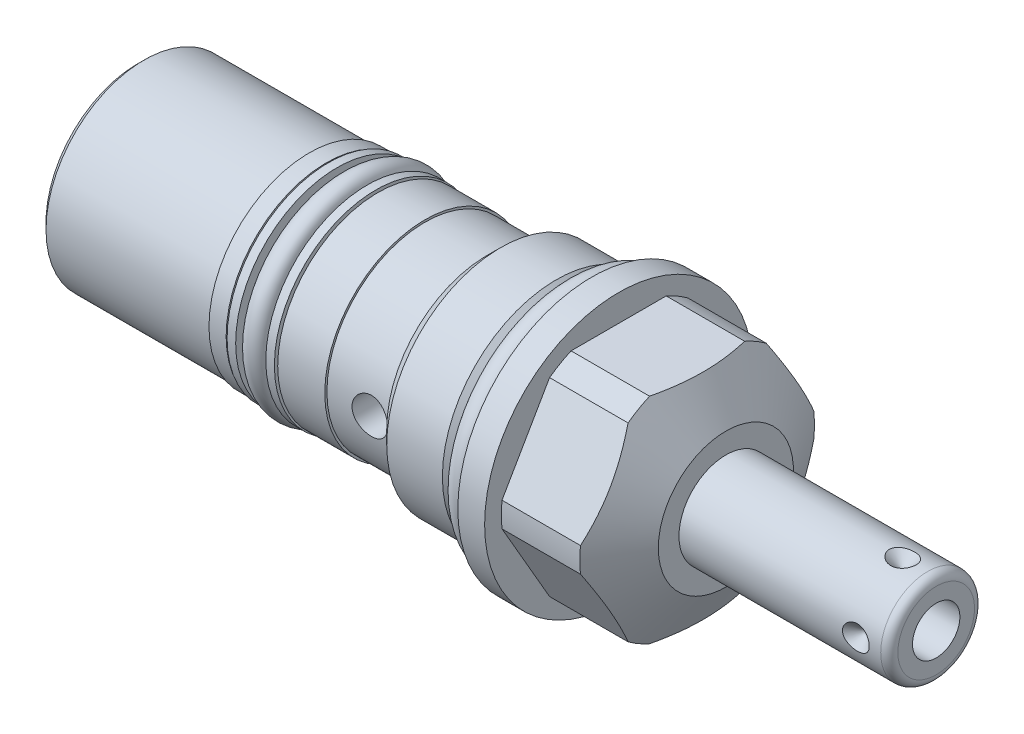
SolidWorks part; units mm, degrees
material "Alloy Steel"
ref_plane "Front Plane" through (0, 0, 0) normal (0, 0, 1) x (1, 0, 0)
ref_plane "Top Plane" through (0, 0, 0) normal (0, 1, 0) x (1, 0, 0)
ref_plane "Right Plane" through (0, 0, 0) normal (1, 0, 0) x (0, 0, -1)
ref_plane "Plane1" through (0, 0, 0) normal (1, 0, 0) x (0, 0, -1)
sketch "Sketch1" plane through (0, 0, 0) normal (1, 0, 0) x (0, 0, -1)
  circle A0 centre (0, 0) radius 15.875
  dimension "D1" = 31.75
extrude "Extrude1" add sketch "Sketch1" along normal blind 15.875 and the other way blind 53.7972
ref_plane "Plane2" through (0, 0, 0) normal (1, 0, 0) x (0, 0, -1)
sketch "Sketch2" plane through (0, 0, 0) normal (1, 0, 0) x (0, 0, -1)
  circle A0 centre (0, 0) radius 13.4937
  circle A1 centre (0, 0) radius 15.875 construction
  circle A2 centre (0, 0) radius 15.875
  dimension "D1" = 26.9875
extrude "Cut-Extrude1" cut sketch "Sketch2" against normal up to next
ref_plane "Plane3" through (0, 0, 0) normal (0, 0, 1) x (1, 0, 0)
sketch "Sketch3" plane through (0, 0, 0) normal (0, 0, 1) x (1, 0, 0)
  line L0 (11.3289, 15.875) -> (15.875, 8.001)
  line L1 (-8.1458, 0) -> (17.0188, 0) construction
  line L2 (15.875, 8.001) -> (15.875, 15.875)
  line L3 (15.875, 15.875) -> (11.3289, 15.875)
  line L4 (15.875, 15.875) -> (0, 15.875) construction
  dimension "D1" = 16.002
  dimension "D2" = 30
revolve "Cut-Revolve1" cut sketch "Sketch3" angle 360 about L1
ref_plane "Plane5" through (3.175, 0, 0) normal (-1, 0, 0) x (0, 0, 1)
sketch "Sketch5" plane through (3.175, 0, 0) normal (-1, 0, 0) x (0, 0, 1)
  line L0 (-7.3323, 12.7) -> (7.3323, 12.7)
  line L1 (7.3323, 12.7) -> (14.6647, 0)
  line L2 (14.6647, 0) -> (7.3323, -12.7)
  line L3 (7.3323, -12.7) -> (-7.3323, -12.7)
  line L4 (-7.3323, -12.7) -> (-14.6647, 0)
  line L5 (-14.6647, 0) -> (-7.3323, 12.7)
  line L6 (0, 0) -> (18.7904, 0) construction
  line L7 (0, 0) -> (7.3323, 12.7) construction
  line L8 (0, 0) -> (-7.3323, 12.7) construction
  circle A0 centre (0, 0) radius 15.875 construction
  circle A1 centre (0, 0) radius 15.875
  dimension "D1" = 25.4
  dimension "D2" = 120
  dimension "D3" = 60
extrude "Cut-Extrude3" cut sketch "Sketch5" against normal up to next
ref_plane "Plane7" through (3.175, 0, 0) normal (-1, 0, 0) x (0, 0, 1)
sketch "Sketch7" plane through (3.175, 0, 0) normal (-1, 0, 0) x (0, 0, 1)
  circle A0 centre (0, 0) radius 13.8938
  circle A1 centre (0, 0) radius 15.875 construction
  circle A2 centre (0, 0) radius 15.875
  dimension "D1" = 27.7876
extrude "Cut-Extrude5" cut sketch "Sketch7" against normal up to next
ref_plane "Plane9" through (0, 0, 0) normal (0, 0, 1) x (1, 0, 0)
sketch "Sketch9" plane through (0, 0, 0) normal (0, 0, 1) x (1, 0, 0)
  line L0 (0, 13.4937) -> (0, 12.0015)
  line L1 (0, 12.0015) -> (-2.7178, 12.0015)
  line L2 (-2.7178, 12.0015) -> (-4.21, 13.4937)
  line L3 (-4.4206, 0) -> (0.2105, 0) construction
  line L4 (0, 13.4937) -> (-4.21, 13.4937)
  line L5 (0, 13.4937) -> (-53.7972, 13.4937) construction
  line L6 (0, 15.875) -> (0, -15.875) construction
  dimension "D1" = 2.7178
  dimension "D2" = 45
  dimension "D3" = 24.003
revolve "Cut-Revolve3" cut sketch "Sketch9" angle 360 about L3
ref_plane "Plane10" through (0, 0, 0) normal (0, 0, 1) x (1, 0, 0)
sketch "Sketch10" plane through (0, 0, 0) normal (0, 0, 1) x (1, 0, 0)
  line L0 (-10.8013, 13.4937) -> (-12.4206, 11.8745)
  line L1 (-12.4206, 11.8745) -> (-53.7972, 11.8745)
  line L2 (-55.947, 0) -> (-8.6516, 0) construction
  line L3 (-2.7178, 12.0015) -> (-2.7178, -12.0015) construction
  line L4 (-53.7972, 13.4937) -> (-53.7972, 11.8745)
  line L6 (-4.21, 13.4937) -> (-53.7972, 13.4937) construction
  line L7 (-10.8013, 13.4937) -> (-53.7972, 13.4937)
  dimension "D1" = 23.749
  dimension "D2" = 45
  dimension "D3" = 9.7028
revolve "Cut-Revolve4" cut sketch "Sketch10" angle 360 about L2
ref_plane "Plane12" through (0, 0, 0) normal (0, 0, 1) x (1, 0, 0)
sketch "Sketch12" plane through (0, 0, 0) normal (0, 0, 1) x (1, 0, 0)
  line L0 (-31.4452, 11.8745) -> (-31.4452, 9.8298)
  line L1 (-31.4452, 9.8298) -> (-25.3365, 9.8298)
  line L2 (-25.3365, 9.8298) -> (-25.3365, 11.8745)
  line L3 (-31.7506, 0) -> (-25.0311, 0) construction
  line L4 (-31.4452, 11.8745) -> (-25.3365, 11.8745)
  line L5 (-12.4206, 11.8745) -> (-53.7972, 11.8745) construction
  line L6 (-53.7972, 11.8745) -> (-53.7972, -11.8745) construction
  dimension "D1" = 6.1087
  dimension "D2" = 19.6596
  dimension "D3" = 22.352
revolve "Cut-Revolve6" cut sketch "Sketch12" angle 360 about L3
ref_plane "Plane14" through (0, 0, 0) normal (0, 0, 1) x (0, -1, 0)
sketch "Sketch14" plane through (0, 0, 0) normal (0, 0, 1) x (0, -1, 0)
  line L0 (11.8745, -53.7972) -> (11.6205, -53.7972)
  line L1 (11.6205, -53.7972) -> (11.6205, -33.4772)
  line L2 (11.6205, -33.4772) -> (11.8745, -33.4772)
  line L3 (11.8745, -33.4772) -> (11.8745, -53.7972)
  line L4 (11.8745, -12.4206) -> (11.6205, -12.4206)
  line L5 (11.6205, -12.4206) -> (11.6205, -19.7612)
  line L6 (11.6205, -19.7612) -> (11.8745, -19.7612)
  line L7 (11.8745, -19.7612) -> (11.8745, -12.4206)
  line L8 (0, -55.866) -> (0, -10.3518) construction
  line L9 (11.8745, -53.7972) -> (11.8745, -31.4452) construction
  line L10 (11.8745, -25.3365) -> (11.8745, -12.4206) construction
  line L11 (-11.8745, -53.7972) -> (11.8745, -53.7972) construction
  dimension "D1" = 13.716
  dimension "D2" = 23.241
  dimension "D3" = 20.32
  dimension "D4" = 7.3406
revolve "Cut-Revolve8" cut sketch "Sketch14" angle 360 about L8
ref_plane "Plane15" through (0, 0, 0) normal (0, 0, 1) x (0, -1, 0)
sketch "Sketch15" plane through (0, 0, 0) normal (0, 0, 1) x (0, -1, 0)
  line L0 (0, -3.0937) -> (0, 0.1473) construction
  line L1 (-15.875, 0) -> (15.875, 0) construction
  circle A0 centre (13.4747, -1.4732) radius 1.4732
  dimension "D1" = 2.9464
  dimension "D2" = 1.4732
  dimension "D3" = 26.9494
revolve "Revolve1" add sketch "Sketch15" angle 360 about L0
ref_plane "Plane16" through (0, 0, 0) normal (0, 0, 1) x (0, -1, 0)
sketch "Sketch16" plane through (0, 0, 0) normal (0, 0, 1) x (0, -1, 0)
  line L0 (9.8298, -25.5905) -> (12.0142, -25.5905)
  line L1 (12.0142, -25.5905) -> (12.0142, -26.6065)
  line L2 (12.0142, -26.6065) -> (9.8298, -26.6065)
  line L3 (9.8298, -26.6065) -> (9.8298, -25.5905)
  line L4 (9.8298, -31.1912) -> (12.0142, -31.1912)
  line L5 (12.0142, -31.1912) -> (12.0142, -30.1752)
  line L6 (12.0142, -30.1752) -> (9.8298, -30.1752)
  line L7 (9.8298, -30.1752) -> (9.8298, -31.1912)
  line L8 (0, -31.4712) -> (0, -25.3105) construction
  line L9 (-11.8745, -25.3365) -> (11.8745, -25.3365) construction
  line L10 (11.8745, -31.4452) -> (-11.8745, -31.4452) construction
  dimension "D1" = 1.016
  dimension "D2" = 19.6596
  dimension "D3" = 24.0284
  dimension "D4" = 0.254
  dimension "D5" = 0.254
revolve "Revolve2" add sketch "Sketch16" angle 360 about L8
ref_plane "Plane17" through (0, 0, 0) normal (0, 0, 1) x (0, -1, 0)
sketch "Sketch17" plane through (0, 0, 0) normal (0, 0, 1) x (0, -1, 0)
  line L0 (0, -31.7506) -> (0, -25.0311) construction
  line L1 (12.0142, -30.1752) -> (-12.0142, -30.1752) construction
  circle A0 centre (11.1379, -28.3909) radius 1.3081
  point P0 (9.8298, -25.3365)
  point P1 (9.8298, -31.4452)
  dimension "D1" = 2.6162
  dimension "D2" = 22.2758
  dimension "D3" = 1.7843
revolve "Revolve3" add sketch "Sketch17" angle 360 about L0
ref_plane "Plane18" through (0, 0, 0) normal (0, 0, 1) x (0, -1, 0)
sketch "S2D0001" plane through (0, 0, 0) normal (0, 0, 1) x (0, -1, 0)
  line L0 (0, 15.875) -> (-5.5562, 15.875)
  line L1 (-5.5562, 15.875) -> (-5.5562, 39.7764)
  line L2 (-4.5402, 40.7924) -> (0, 40.7924)
  line L3 (0, 40.7924) -> (0, 15.875)
  line L4 (0, 7.2658) -> (0, 37.3443) construction
  line L5 (8.001, 15.875) -> (-8.001, 15.875) construction
  line L6 (-15.875, 0) -> (15.875, 0) construction
  arc A0 (-4.5402, 40.7924) -> (-5.5562, 39.7764) centre (-4.5402, 39.7764) ccw
  dimension "D2" = 1.016
  dimension "D1" = 11.1125
  dimension "D3" = 40.7924
revolve "Revolve4" add sketch "S2D0001" angle 360 about L4
ref_plane "Plane19" through (36.322, -2.8067, 0) normal (0, 0, 1) x (0, -1, 0)
sketch "Sketch19" plane through (36.322, -2.8067, 0) normal (0, 0, 1) x (0, -1, 0)
  line L0 (0, 4.4704) -> (0, -5.6896)
  line L1 (0, -5.6896) -> (-2.8067, -7.376)
  line L2 (0, 4.4704) -> (-2.8067, 4.4704)
  line L3 (-2.8067, 4.4704) -> (-2.8067, -7.376)
  line L4 (-2.8067, -18.6227) -> (-2.8067, 0.5923) construction
  line L5 (1.7335, 4.4704) -> (-7.3469, 4.4704) construction
  dimension "D1" = 5.6134
  dimension "D2" = 10.16
  dimension "D3" = 59
revolve "Cut-Revolve9" cut sketch "Sketch19" angle 360 about L4
ref_plane "Plane20" through (32.3596, 0, -5.5562) normal (0, 1, 0) x (1, 0, 0)
sketch "S2D0002" plane through (32.3596, 0, -5.5562) normal (0, 1, 0) x (1, 0, 0)
  line L0 (4.4704, 0) -> (6.0579, 0)
  line L1 (6.0579, 0) -> (4.4704, -1.5875)
  line L2 (4.4704, 0) -> (4.4704, -1.5875)
  line L3 (4.4704, -3.3652) -> (4.4704, 0.0794) construction
  line L4 (7.4168, 0) -> (-16.4846, 0) construction
  line L5 (8.4328, -10.0965) -> (8.4328, -1.016) construction
  dimension "D1" = 3.9624
  dimension "D2" = 45
  dimension "D3" = 3.175
revolve "Cut-Revolve10" cut sketch "S2D0002" angle 360 about L3
pattern_circular "CirPattern1" count 4 over 360 about axis through (7.2658, 0, 0) along (-1, 0, 0) of "Cut-Revolve10"
chamfer "Chamfer1" distance 0.762 angle 45 1 edges at (-53.7972, 0, 11.6205)
sketch "Sketch22" plane through (-53.7972, 0, 0) normal (-1, 0, 0) x (0, 0, 1)
  circle A0 centre (0, 0) radius 0.8001
  dimension "D1" = 1.6002
extrude "Cut-Extrude6" cut sketch "Sketch22" against normal blind 0.762
sketch "Sketch23" plane through (0, 0, 0) normal (0, 0, 1) x (1, 0, 0)
  line L0 (-53.7972, 10.8585) -> (-53.7972, -10.8585) construction
  circle A0 centre (-14.6812, 0) radius 2.1082
  dimension "D1" = 4.2164
  dimension "D2" = 39.116
extrude "Cut-Extrude7" cut sketch "Sketch23" along normal through all
